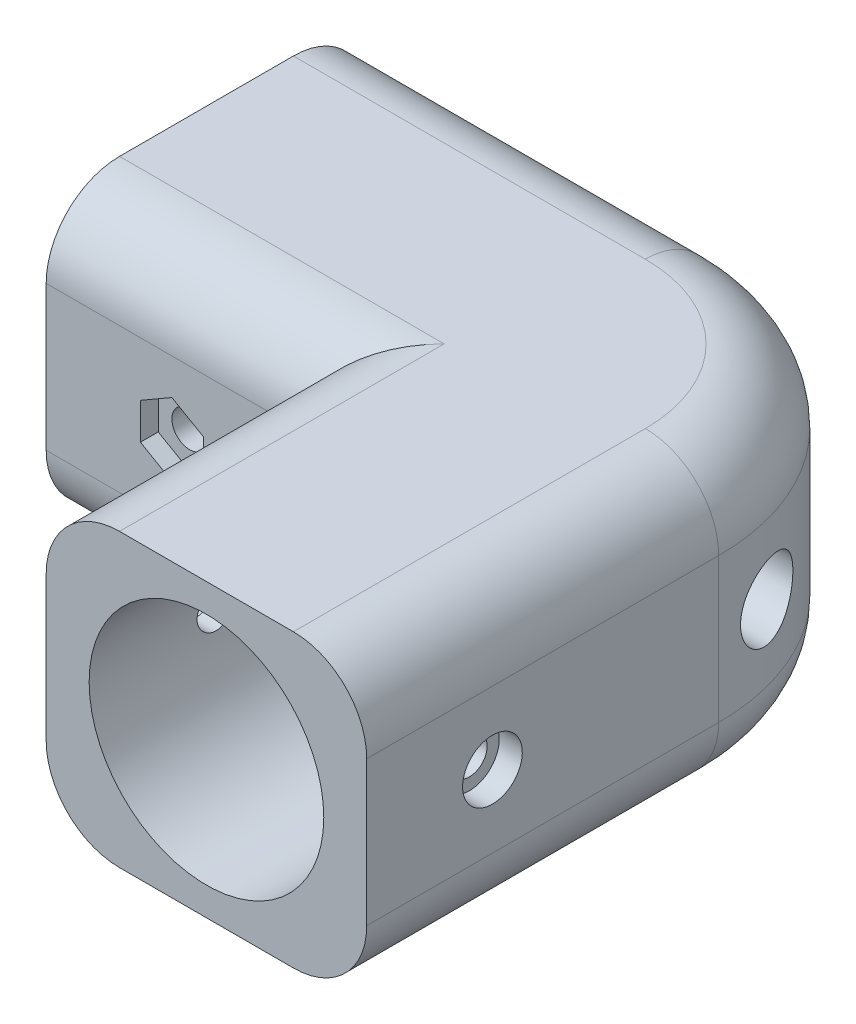
SolidWorks part; units mm, degrees
ref_plane "Front Plane" through (0, 0, 0) normal (0, 0, 1) x (1, 0, 0)
ref_plane "Top Plane" through (0, 0, 0) normal (0, 1, 0) x (1, 0, 0)
ref_plane "Right Plane" through (0, 0, 0) normal (1, 0, 0) x (0, 0, -1)
sketch "Sketch1" plane through (0, 0, 0) normal (0, 0, 1) x (1, 0, 0)
  circle A0 centre (0, 0) radius 11.2
  circle A1 centre (0, 0) radius 13.9
  dimension "D1" = 22.4
  dimension "D2" = 2.7
extrude "Boss-Extrude1" add sketch "Sketch1" along normal blind 7
sketch "Sketch2" plane through (0, 0, 7) normal (0, 0, 1) x (1, 0, 0)
  line L1 (-15.3, 13.9) -> (15.3, 13.9)
  line L2 (-15.3, 13.9) -> (-15.3, -13.9)
  line L3 (-15.3, -13.9) -> (15.3, -13.9)
  line L4 (15.3, 13.9) -> (15.3, -13.9)
  circle A0 centre (0, 0) radius 13.9 construction
  circle A1 centre (0, 0) radius 11.2 construction
  circle A2 centre (0, 0) radius 11.2
  dimension "D1" = 15.3
  dimension "D2" = 15.3
extrude "Boss-Extrude2" add sketch "Sketch2" against normal blind 24
sketch "Sketch6" plane through (-15.3, 0, 0) normal (-1, 0, 0) x (0, 0, 1)
  line L1 (-17, 13.9) -> (-17, -13.9) construction
  line L2 (-17, 13.9) -> (7, 13.9) construction
  line L3 (-47.6, 13.9) -> (-17, 13.9)
  line L4 (-47.6, 13.9) -> (-47.6, -13.9)
  line L5 (-47.6, -13.9) -> (-17, -13.9)
  line L6 (-17, 13.9) -> (-17, -13.9)
  line L7 (-17, -13.9) -> (7, -13.9) construction
  circle A0 centre (-32.3, 0) radius 11.2
  circle A1 centre (-32.3, 0) radius 13.9
  line M8 (-17, 13.9) -> (-17, -13.9)
  dimension "D1" = 22.4
  dimension "D2" = 2.7
  dimension "D3" = 15.3
  dimension "D4" = 15.3
extrude "Boss-Extrude6" add sketch "Sketch6" along normal blind 24 separate body contours A1 L3 M8 | A1 L3 L4 | A1 L4 L5 | A1 L5 L6 | A1 A0
sketch "Sketch7" plane through (0, 13.9, 0) normal (0, 1, 0) x (1, 0, 0)
  line L0 (15.3, 17) -> (15.3, -7) construction
  line L1 (-15.3, 17) -> (15.3, 17)
  line L2 (-15.3, 17) -> (-15.3, 47.6)
  line L3 (-15.3, 47.6) -> (15.3, 47.6)
  line L4 (15.3, 17) -> (15.3, 47.6)
  line L5 (-39.3, 47.6) -> (-15.3, 47.6) construction
extrude "Boss-Extrude7" add sketch "Sketch7" against normal up to surface (27.8 mm away) up to face at (-27.3, -13.9, -32.3)
fillet "Fillet1" radius 21 1 edges at (15.3, 0, -47.6)
fillet "Fillet2" radius 7 10 edges at (15.3, -13.9, -9.8) (9.1492, -13.9, -41.4492) (15.3, 13.9, -9.8) (9.1492, 13.9, -41.4492) (-15.3, -13.9, -5) (-27.3, -13.9, -17) (-15.3, 13.9, -5) (-27.3, 13.9, -17) (-22.5, -13.9, -47.6) (-22.5, 13.9, -47.6)
sketch "Sketch8" plane through (-15.3, 0, 0) normal (-1, 0, 0) x (0, 0, 1)
  circle A0 centre (-32.3, 0) radius 3.5
  circle A1 centre (-32.3, 0) radius 11.2 construction
  dimension "D1" = 7
extrude "Cut-Extrude1" cut sketch "Sketch8" against normal through all
sketch "Sketch9" plane through (0, 0, -17) normal (0, 0, 1) x (1, 0, 0)
  circle A0 centre (0, 0) radius 3.5
  dimension "D1" = 7
extrude "Cut-Extrude2" cut sketch "Sketch9" against normal through all
sketch "Sketch11" plane through (-15.3, 0, 0) normal (-1, 0, 0) x (0, 0, 1)
  line L0 (7, 6.9) -> (7, -6.9) construction
  line L1 (-2, -1.7321) -> (-2, 1.7321)
  line L2 (-2, 1.7321) -> (-5, 3.4641)
  line L3 (-5, 3.4641) -> (-8, 1.7321)
  line L4 (-8, 1.7321) -> (-8, -1.7321)
  line L5 (-8, -1.7321) -> (-5, -3.4641)
  line L6 (-5, -3.4641) -> (-2, -1.7321)
  line L7 (7, 6.9) -> (-17, 6.9) construction
  circle A0 centre (-5, 0) radius 3 construction
  point P17 (-5, 6.9)
  dimension "D1" = 6
extrude "Cut-Extrude3" cut sketch "Sketch11" against normal blind 2.2
sketch "Sketch12" plane through (-13.1, 0, 0) normal (-1, 0, 0) x (0, 0, 1)
  circle A0 centre (-5, 0) radius 1.7
  dimension "D1" = 3.4
extrude "Cut-Extrude4" cut sketch "Sketch12" against normal through all
sketch "Sketch13" plane through (15.3, 0, 0) normal (1, 0, 0) x (0, 0, -1)
  circle A0 centre (5, 0) radius 2.85
  dimension "D1" = 5.7
extrude "Cut-Extrude5" cut sketch "Sketch13" against normal blind 2.2
sketch "Sketch15" plane through (0, 0, -17) normal (0, 0, 1) x (1, 0, 0)
  line L0 (-15.3, 6.9) -> (-39.3, 6.9) construction
  line L1 (-24.3, -1.7321) -> (-24.3, 1.7321)
  line L2 (-24.3, 1.7321) -> (-27.3, 3.4641)
  line L3 (-27.3, 3.4641) -> (-30.3, 1.7321)
  line L4 (-30.3, 1.7321) -> (-30.3, -1.7321)
  line L5 (-30.3, -1.7321) -> (-27.3, -3.4641)
  line L6 (-27.3, -3.4641) -> (-24.3, -1.7321)
  line L7 (-39.3, 6.9) -> (-39.3, -6.9) construction
  circle A0 centre (-27.3, 0) radius 3 construction
  point P12 (-27.3, 6.9)
  point P16 (-39.3, 0)
  dimension "D1" = 6
extrude "Cut-Extrude6" cut sketch "Sketch15" against normal blind 1.7
sketch "Sketch16" plane through (0, 0, -18.7) normal (0, 0, 1) x (1, 0, 0)
  line L1 (-30.3, 1.7321) -> (-30.3, -1.7321) construction
  circle A0 centre (-27.3, 0) radius 1.7
  point P7 (-30.3, 0)
  dimension "D1" = 3.4
extrude "Cut-Extrude7" cut sketch "Sketch16" against normal through all
sketch "Sketch17" plane through (0, 0, -47.6) normal (0, 0, -1) x (-1, 0, 0)
  circle A0 centre (27.3, 0) radius 2.85
  dimension "D1" = 5.7
extrude "Cut-Extrude8" cut sketch "Sketch17" against normal blind 1.7
